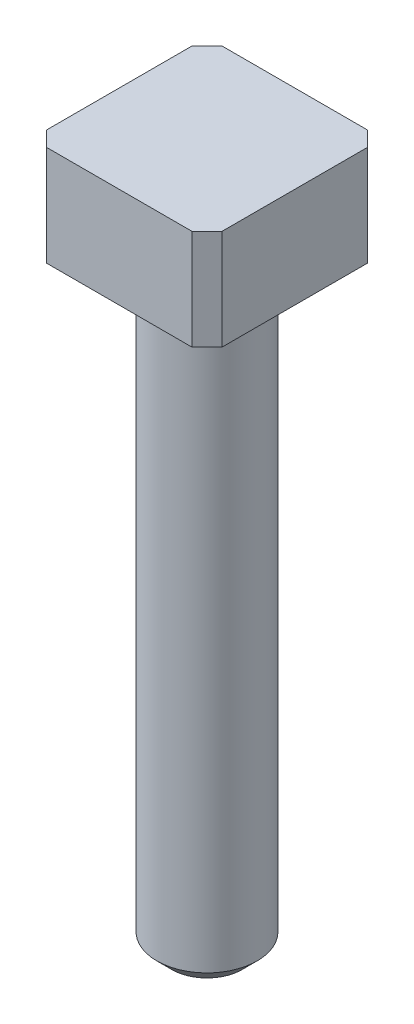
SolidWorks part; units mm, degrees
ref_plane "Front Plane" through (0, 0, 0) normal (0, 0, 1) x (1, 0, 0)
ref_plane "Top Plane" through (0, 0, 0) normal (0, 1, 0) x (1, 0, 0)
ref_plane "Right Plane" through (0, 0, 0) normal (1, 0, 0) x (0, 0, -1)
sketch "Sketch1" plane through (0, 0, 0) normal (0, 1, 0) x (1, 0, 0)
  line L1 (1.75, -1.75) -> (-1.75, -1.75)
  line L2 (1.75, -1.75) -> (1.75, 1.75)
  line L3 (1.75, 1.75) -> (-1.75, 1.75)
  line L4 (-1.75, -1.75) -> (-1.75, 1.75)
  line L5 (1.75, -1.75) -> (-1.75, 1.75) construction
  line L6 (1.75, 1.75) -> (-1.75, -1.75) construction
  point P0 (0, 0)
  dimension "D1" = 3.5
  dimension "D2" = 3.5
extrude "Boss-Extrude1" add sketch "Sketch1" along normal blind 2
sketch "Sketch2" plane through (0, 0, 0) normal (0, 1, 0) x (1, 0, 0)
  circle A0 centre (0, 0) radius 1
  dimension "D1" = 2
extrude "Boss-Extrude2" add sketch "Sketch2" against normal blind 12
chamfer "Chamfer1" distance 0.3 angle 45 5 edges at (-1.75, 1, 1.75) (-1.75, 1, -1.75) (1.75, 1, 1.75) (1.75, 1, -1.75) (0, -12, 1)
